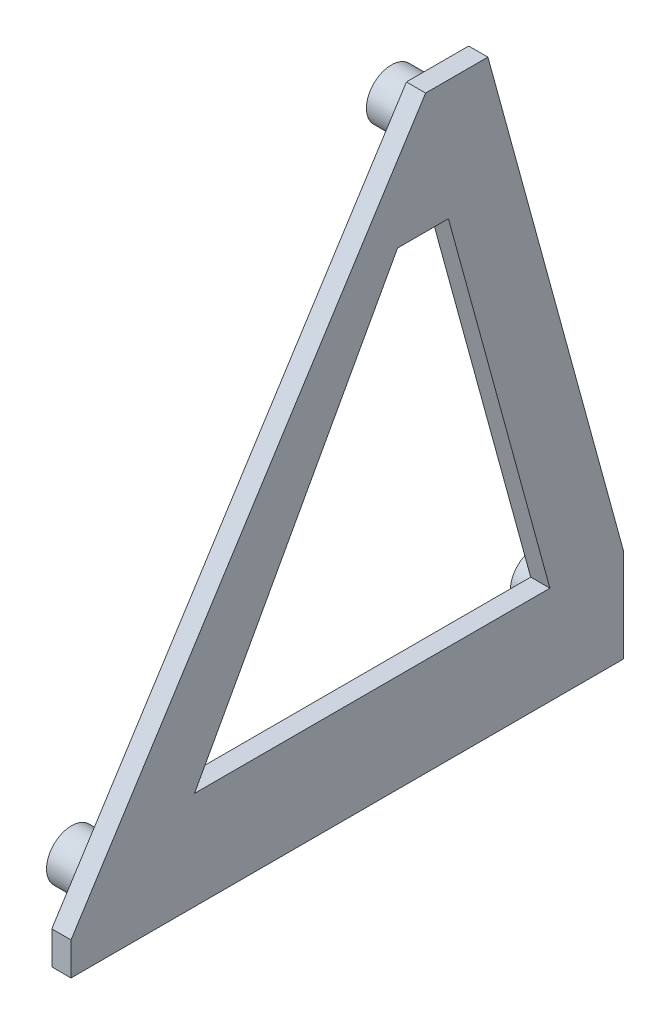
SolidWorks part; units mm, degrees
ref_plane "前视基准面" through (0, 0, 0) normal (0, 0, 1) x (1, 0, 0)
ref_plane "上视基准面" through (0, 0, 0) normal (0, 1, 0) x (1, 0, 0)
ref_plane "右视基准面" through (0, 0, 0) normal (1, 0, 0) x (0, 0, -1)
sketch "草图1" plane through (0, 0, 0) normal (1, 0, 0) x (0, 0, -1)
  line L1 (-37.9063, 40.357) -> (25.6458, 40.357)
  line L2 (-37.9063, 40.357) -> (-37.9063, -34.8247)
  line L3 (-37.9063, -34.8247) -> (25.6458, -34.8247)
  line L4 (25.6458, 40.357) -> (25.6458, -34.8247)
  point P4 (-37.9063, -34.8247)
  dimension "D1" = 63.552
  dimension "D2" = 75.1817
extrude "凸台-拉伸1" add sketch "草图1" along normal blind 2
sketch "草图2" plane through (2, 0, 0) normal (1, 0, 0) x (0, 0, -1)
  line L0 (-37.9063, 40.357) -> (-37.9063, -34.8247) construction
  circle A0 centre (6.2958, 33.8767) radius 1.5
  circle A1 centre (-27.0063, -18.0643) radius 1.5
  circle A2 centre (21.2834, -17.0643) radius 1.5
  circle A3 centre (6.2958, 33.8767) radius 2.6
  circle A4 centre (-27.0063, -18.0643) radius 2.6
  circle A5 centre (21.2834, -17.0643) radius 2.6
  dimension "D1" = 10.9
  dimension "D2" = 1
  dimension "D3" = 61.7
  dimension "D4" = 53.1
  dimension "D5" = 48.3
sketch "草图3" plane through (2, 0, 0) normal (1, 0, 0) x (0, 0, -1)
  line L0 (3.8616, 38.1572) -> (-33.0549, -19.7346)
  line L2 (-37.9063, 40.357) -> (-37.9063, -34.8247) construction
  line L3 (-37.9063, -19.7346) -> (-37.9063, 40.357)
  line L4 (-37.9063, 40.357) -> (25.6458, 40.357)
  line L5 (25.6458, 40.357) -> (25.6458, -13.4038)
  line L6 (25.6458, 40.357) -> (25.6458, -34.8247) construction
  line L8 (24.4555, -13.4038) -> (10.3449, 38.1572)
  line L9 (10.3449, 38.1572) -> (3.8616, 38.1572)
  line L10 (-33.0549, -23.1669) -> (24.4555, -23.1669)
  line L11 (25.6458, -23.1669) -> (25.6458, -34.8247)
  line L12 (25.6458, -34.8247) -> (-37.9063, -34.8247)
  line L13 (-37.9063, -34.8247) -> (-37.9063, -23.1669)
  line L14 (-33.0549, -19.7346) -> (-33.0549, -23.1669)
  line L15 (-37.9063, -19.7346) -> (-37.9063, -23.1669)
  line L16 (24.4555, -13.4038) -> (24.4555, -23.1669)
  line L17 (25.6458, -13.4038) -> (25.6458, -23.1669)
extrude "切除-拉伸3" cut sketch "草图3" against normal blind 2
sketch "草图4" plane through (2, 0, 0) normal (1, 0, 0) x (0, 0, -1)
  line L0 (0.937, 25.6441) -> (-20.2045, -12.9535)
  line L1 (-20.2045, -12.9535) -> (16.8003, -12.9535)
  line L2 (16.8003, -12.9535) -> (6.2353, 25.6441)
  line L3 (6.2353, 25.6441) -> (0.937, 25.6441)
extrude "切除-拉伸4" cut sketch "草图4" against normal blind 2
extrude "凸台-拉伸2" add sketch "草图2" against normal blind 6
